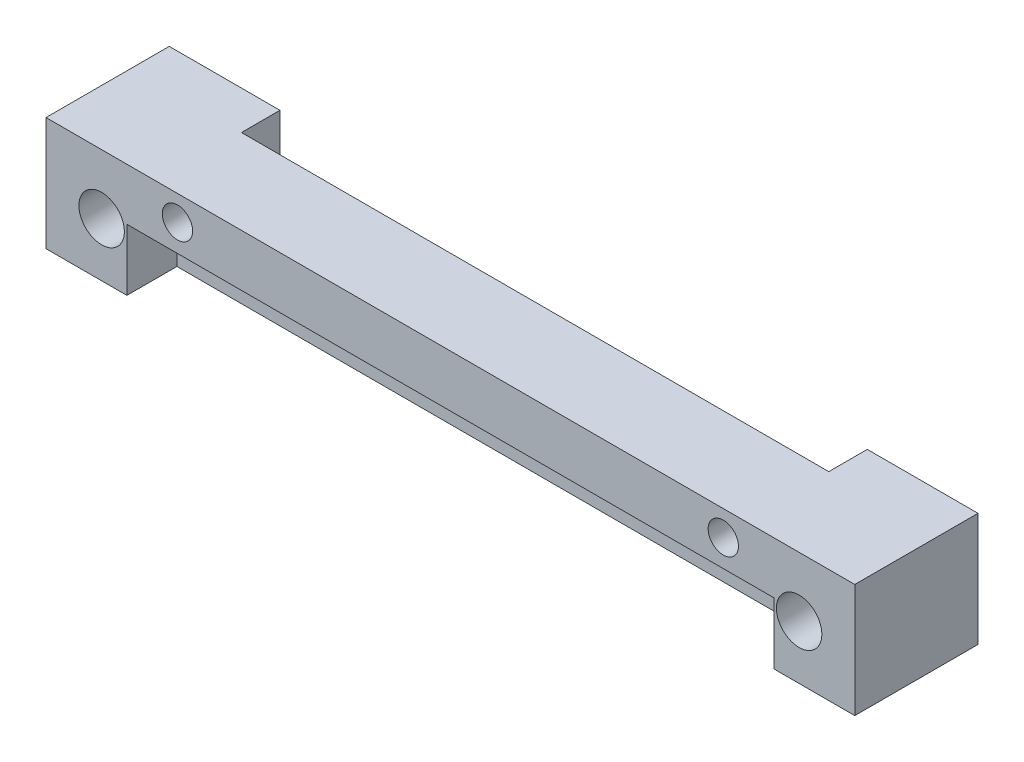
SolidWorks part; units mm, degrees
ref_plane "Front Plane" through (0, 0, 0) normal (0, 0, 1) x (1, 0, 0)
ref_plane "Top Plane" through (0, 0, 0) normal (0, 1, 0) x (1, 0, 0)
ref_plane "Right Plane" through (0, 0, 0) normal (1, 0, 0) x (0, 0, -1)
ref_plane "Plane1" through (0, 0.508, 0) normal (0, 1, 0) x (1, 0, 0)
sketch "Sketch1" plane through (0, 0.508, 0) normal (0, 1, 0) x (1, 0, 0)
  line L1 (-26.67, 4.445) -> (26.67, 4.445)
  line L2 (-26.67, 4.445) -> (-26.67, -4.445)
  line L3 (-26.67, -4.445) -> (26.67, -4.445)
  line L4 (26.67, 4.445) -> (26.67, -4.445)
  line L5 (-26.67, 4.445) -> (26.67, -4.445) construction
  line L6 (-26.67, -4.445) -> (26.67, 4.445) construction
  point P0 (0, 0)
  dimension "D1" = 53.34
  dimension "D2" = 8.89
extrude "16x19mm bar sawn in half width wise" add sketch "Sketch1" along normal blind 15.4686
sketch "Sketch2" plane through (0, 0, 4.445) normal (0, 0, 1) x (1, 0, 0)
  line L1 (-26.67, 15.9766) -> (26.67, 15.9766)
  line L2 (-26.67, 15.9766) -> (-26.67, 0.508)
  line L3 (-26.67, 0.508) -> (26.67, 0.508)
  line L4 (26.67, 15.9766) -> (26.67, 0.508)
  line L5 (-26.67, 15.9766) -> (26.67, 0.508) construction
  line L6 (-26.67, 0.508) -> (26.67, 15.9766) construction
  point P4 (0, 8.2423)
extrude "Cut-Extrude1" cut sketch "Sketch2" against normal blind 0.762
sketch "Sketch4" plane through (0, 15.9766, 0) normal (0, 1, 0) x (1, 0, 0)
  line L1 (-26.67, -3.683) -> (26.67, -3.683)
  line L2 (-26.67, -3.683) -> (-26.67, 4.445)
  line L3 (-26.67, 4.445) -> (26.67, 4.445)
  line L4 (26.67, -3.683) -> (26.67, 4.445)
  line L5 (-26.67, -3.683) -> (26.67, 4.445) construction
  line L6 (-26.67, 4.445) -> (26.67, -3.683) construction
  point P4 (0, 0.381)
extrude "Cut-Extrude2" cut sketch "Sketch4" against normal blind 7.9756
sketch "Sketch5" plane through (0, 0, 0) normal (1, 0, 0) x (0, 0, -1)
  line L0 (-3.683, 0.508) -> (-3.683, 8.001) construction
  line L1 (-0.381, 0.508) -> (-3.683, 0.508)
  line L2 (-0.381, 0.508) -> (-0.381, 4.572)
  line L3 (-0.381, 4.572) -> (-3.683, 4.572)
  line L4 (-3.683, 0.508) -> (-3.683, 4.572)
  line L5 (-0.381, 0.508) -> (-3.683, 4.572) construction
  line L6 (-0.381, 4.572) -> (-3.683, 0.508) construction
  line L7 (-3.683, 0.508) -> (4.445, 0.508) construction
  point P4 (-2.032, 2.54)
  dimension "D1" = 3.302
  dimension "D2" = 4.064
extrude "Cut-Extrude3" cut sketch "Sketch5" against normal blind 21.336 and the other way blind 21.336
sketch "Sketch6" plane through (0, 0, -4.445) normal (0, 0, -1) x (-1, 0, 0)
  line L1 (-26.67, 8.001) -> (-26.67, 0.508) construction
  line L2 (-26.67, 0.508) -> (26.67, 0.508) construction
  circle A0 centre (23, 4.064) radius 1.4986
  circle A1 centre (-23, 4.064) radius 1.4986
  dimension "D1" = 2.9972
  dimension "D2" = 2.9972
  dimension "D3" = 3.67
  dimension "D4" = 49.67
  dimension "D5" = 3.556
extrude "M3 Clearance" cut sketch "Sketch6" against normal up to next
sketch "Sketch7" plane through (0, 0, 0) normal (0, 0, 1) x (1, 0, 0)
  circle A0 centre (18, 6.3436) radius 1
  circle A1 centre (-18, 6.3436) radius 1
extrude "Tapped M2" cut sketch "Sketch7" against normal through all both and the other way through all
sketch "Sketch10" plane through (0, 0, -4.445) normal (0, 0, -1) x (-1, 0, 0)
  line L0 (-26.67, 8.001) -> (26.67, 8.001) construction
  line L1 (-19.3675, 8.001) -> (19.3675, 8.001)
  line L2 (-19.3675, 8.001) -> (-19.3675, 0.508)
  line L3 (-19.3675, 0.508) -> (19.3675, 0.508)
  line L4 (19.3675, 8.001) -> (19.3675, 0.508)
  line L5 (-19.3675, 8.001) -> (19.3675, 0.508) construction
  line L6 (-19.3675, 0.508) -> (19.3675, 8.001) construction
  line L7 (-26.67, 0.508) -> (26.67, 0.508) construction
  line L8 (0, 55) -> (0, -55) construction
  point P4 (0, 4.2545)
  dimension "D1" = 38.735
extrude "Cut-Extrude6" cut sketch "Sketch10" against normal blind 2.54
